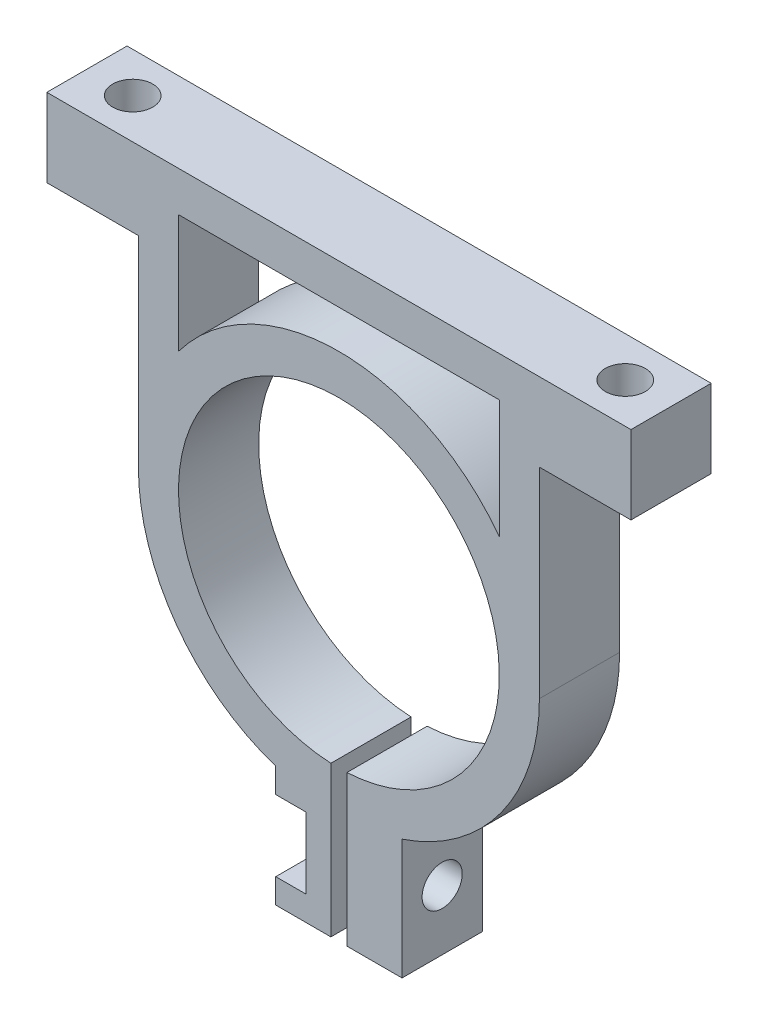
SolidWorks part; units mm, degrees
ref_plane "Top Plane" through (0, 0, 0) normal (0, 0, 1) x (1, 0, 0)
ref_plane "Front Plane" through (0, 0, 0) normal (0, 1, 0) x (1, 0, 0)
ref_plane "Right Plane" through (0, 0, 0) normal (1, 0, 0) x (0, 0, -1)
sketch "Profile Sketch" plane through (0, 0, 0) normal (0, 0, 1) x (1, 0, 0)
  line L0 (-15.875, 0) -> (-15.875, 15.875)
  line L1 (-23.125, 15.875) -> (-15.875, 15.875)
  line L2 (-23.125, 15.875) -> (-23.125, 22.075)
  line L3 (-23.125, 22.075) -> (23.125, 22.075)
  line L4 (23.125, 15.875) -> (23.125, 22.075)
  line L5 (-23.125, 15.875) -> (23.125, 22.075) construction
  line L6 (-23.125, 22.075) -> (23.125, 15.875) construction
  line L7 (15.875, 0) -> (15.875, 15.875)
  line L8 (15.875, 15.875) -> (23.125, 15.875)
  line L9 (-5, -15.067) -> (-5, -24.592)
  line L12 (-5, -24.592) -> (5, -24.592)
  line L15 (-5, -24.592) -> (0, -12.7) construction
  line L16 (0, -12.7) -> (5, -24.592) construction
  line L17 (5, -15.067) -> (5, -24.592)
  circle A0 centre (0, 0) radius 12.7
  arc A1 (-15.875, 0) -> (-5, -15.067) centre (0, 0) ccw
  arc A2 (5, -15.067) -> (15.875, 0) centre (0, 0) ccw
  point P3 (0, -12.7)
  point P4 (0, 18.975)
  dimension "D1" = 25.4
  dimension "D2" = 3.175
  dimension "D3" = 6.2
  dimension "D4" = 46.25
  dimension "D5" = 9.525
  dimension "D6" = 10
  dimension "D7" = 5
extrude "Profile Extrude" add sketch "Profile Sketch" along normal blind 6.35
sketch "Gap Sketch" plane through (0, 0, 6.35) normal (0, 0, 1) x (1, 0, 0)
  line L1 (-0.635, -26.1023) -> (0.635, -26.1023)
  line L2 (-0.635, -26.1023) -> (-0.635, -8.9497)
  line L3 (-0.635, -8.9497) -> (0.635, -8.9497)
  line L4 (0.635, -26.1023) -> (0.635, -8.9497)
  line L5 (-0.635, -26.1023) -> (0.635, -8.9497) construction
  line L6 (-0.635, -8.9497) -> (0.635, -26.1023) construction
  point P0 (0, -17.526)
  dimension "D1" = 17.526
  dimension "D2" = 17.1526
  dimension "D3" = 1.27
extrude "Gap Cut" cut sketch "Gap Sketch" against normal through all
sketch "Crossbolt Hole Sketch" plane through (5, 0, 0) normal (1, 0, 0) x (0, 0, -1)
  line L0 (-6.35, -19.8295) -> (0, -19.8295) construction
  line L1 (-6.35, -24.592) -> (-6.35, -15.067) construction
  line L2 (0, -24.592) -> (0, -15.067) construction
  circle A0 centre (-3.175, -19.8295) radius 1.5875
  dimension "D1" = 3.175
extrude "Crossbolt Hole Cut" cut sketch "Crossbolt Hole Sketch" against normal up to surface (10 mm away) up to face at (-5, -19.8295, 3.175)
sketch "Nut Capture Pocket Sketch" plane through (0, 0, 6.35) normal (0, 0, 1) x (1, 0, 0)
  line L0 (-5, -15.067) -> (-5, -24.592) construction
  line L1 (-7.4, -22.643) -> (-2.6, -22.643)
  line L2 (-7.4, -22.643) -> (-7.4, -17.016)
  line L3 (-7.4, -17.016) -> (-2.6, -17.016)
  line L4 (-2.6, -22.643) -> (-2.6, -17.016)
  line L5 (-7.4, -22.643) -> (-2.6, -17.016) construction
  line L6 (-7.4, -17.016) -> (-2.6, -22.643) construction
  point P0 (-5, -19.8295)
  dimension "D1" = 4.8
  dimension "D2" = 5.627
extrude "Nut Capture Pocket Cut" cut sketch "Nut Capture Pocket Sketch" against normal up to surface (6.35 mm away) up to face at (0, -1.5219, 0)
sketch "Mounting Hole Sketch" plane through (0, 15.875, 0) normal (0, -1, 0) x (1, 0, 0)
  line L0 (15.875, 3.175) -> (23.125, 3.175) construction
  line L1 (15.875, 6.35) -> (15.875, 0) construction
  line L2 (23.125, 6.35) -> (23.125, 0) construction
  line L3 (-23.125, 3.175) -> (-15.875, 3.175) construction
  line L4 (-23.125, 6.35) -> (-23.125, 0) construction
  line L5 (-15.875, 6.35) -> (-15.875, 0) construction
  circle A0 centre (19.5, 3.175) radius 1.5875
  circle A1 centre (-19.5, 3.175) radius 1.5875
  dimension "D1" = 3.175
  dimension "D2" = 3.175
extrude "Mounting Hole Cut" cut sketch "Mounting Hole Sketch" against normal up to surface (6.2 mm away) up to face at (0, 22.075, 3.175)
sketch "Lightening Pocket Sketch" plane through (0, 0, 6.35) normal (0, 0, 1) x (1, 0, 0)
  line L2 (23.125, 18.9) -> (-23.125, 18.9)
  line L3 (12.7, 18.9) -> (-12.7, 18.9)
  line L5 (-12.7, 15.875) -> (-12.7, 0)
  line L6 (-12.7, 18.9) -> (-12.7, 9.525)
  line L8 (12.7, 0) -> (12.7, 15.875)
  line L9 (12.7, 9.525) -> (12.7, 18.9)
  arc A2 (0.7937, -15.8551) -> (-0.7938, -15.8551) centre (0, 0) ccw
  arc A3 (12.7, 9.525) -> (-12.7, 9.525) centre (0, 0) ccw
  dimension "D1" = 3.175
  dimension "D2" = 3.175
  dimension "D3" = 3.175
  dimension "D4" = 3.175
extrude "Lightening Pocket Cut" cut sketch "Lightening Pocket Sketch" against normal up to surface (6.35 mm away) up to face at (-0.76, -5.1835, 0)
equation "\"D7@Profile Sketch\"=\"D6@Profile Sketch\"/2"
equation "\"D2@Mounting Hole Sketch\"=\"D1@Mounting Hole Sketch\""
